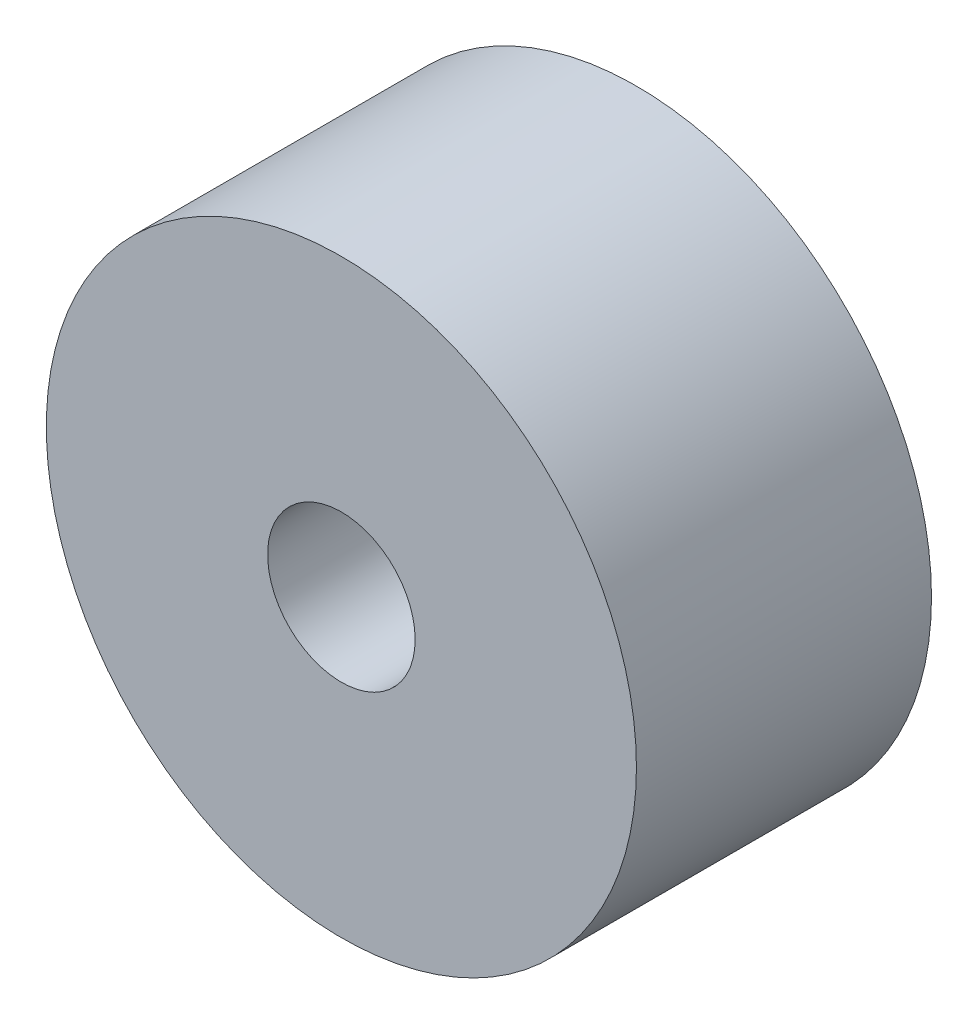
SolidWorks part; units mm, degrees
material "Acrylic (Medium-high impact)"
ref_plane "Front Plane" through (0, 0, 0) normal (0, 0, 1) x (1, 0, 0)
ref_plane "Top Plane" through (0, 0, 0) normal (0, 1, 0) x (1, 0, 0)
ref_plane "Right Plane" through (0, 0, 0) normal (1, 0, 0) x (0, 0, -1)
sketch "Sketch1" plane through (0, 0, 0) normal (0, 0, 1) x (1, 0, 0)
  circle A0 centre (0, 0) radius 6
  circle A1 centre (0, 0) radius 1.5
  dimension "D1" = 12
  dimension "D2" = 3
extrude "Boss-Extrude1" add sketch "Sketch1" along normal blind 6
